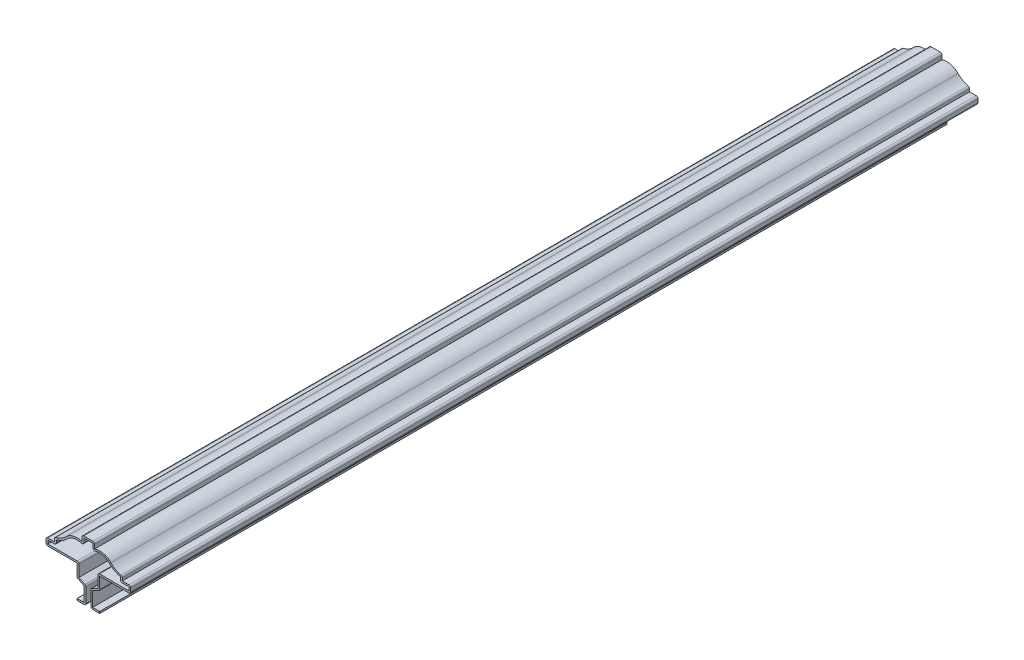
SolidWorks part; units mm, degrees
ref_plane "Front Plane" through (0, 0, 0) normal (0, 0, 1) x (1, 0, 0)
ref_plane "Top Plane" through (0, 0, 0) normal (0, 1, 0) x (1, 0, 0)
ref_plane "Right Plane" through (0, 0, 0) normal (1, 0, 0) x (0, 0, -1)
sketch "Sketch1" plane through (0, 0, 0) normal (0, 0, 1) x (1, 0, 0)
  line L0 (0, 0) -> (0, 32.3215) construction
  line L1 (-6.35, 0) -> (-2.3813, 0)
  line L2 (-2.3813, 0) -> (-2.3813, 8.1121)
  line L3 (-2.3813, 8.1121) -> (-6.35, 10.0965)
  line L4 (-6.35, 10.0965) -> (-6.35, 17.2402)
  line L5 (-6.35, 17.2402) -> (-23.8125, 17.2402)
  line L6 (-23.8125, 17.2402) -> (-23.8125, 21.209)
  line L7 (-23.8125, 21.209) -> (-19.05, 21.209)
  line L8 (-19.05, 21.209) -> (-19.05, 23.5902)
  line L9 (3.5719, 32.3215) -> (-3.5719, 32.3215)
  line L10 (-3.5719, 32.3215) -> (-3.5719, 29.0896)
  line L11 (6.35, 0) -> (2.3813, 0)
  line L12 (2.3813, 0) -> (2.3813, 8.1121)
  line L13 (2.3813, 8.1121) -> (6.35, 10.0965)
  line L14 (6.35, 10.0965) -> (6.35, 17.2402)
  line L15 (6.35, 17.2402) -> (23.8125, 17.2402)
  line L16 (23.8125, 17.2402) -> (23.8125, 21.209)
  line L17 (23.8125, 21.209) -> (19.05, 21.209)
  line L18 (19.05, 21.209) -> (19.05, 23.5902)
  line L19 (3.5719, 32.3215) -> (3.5719, 29.0896)
  arc A0 (-19.05, 23.5902) -> (-12.6337, 26.8742) centre (-20.6312, 34.5897) ccw
  arc A1 (-12.6337, 26.8742) -> (-3.5719, 29.0896) centre (-6.35, 20.8121) cw
  arc A2 (19.05, 23.5902) -> (12.6337, 26.8742) centre (20.6312, 34.5897) cw
  arc A3 (12.6337, 26.8742) -> (3.5719, 29.0896) centre (6.35, 20.8121) ccw
  point P1 (-8.4239, 0)
  point P18 (0, 0)
  point P19 (0.0427, 26.9391)
  point P20 (-2.3813, 9.1281)
  point P21 (-6.35, 12.5794)
  point P22 (-17.5022, 22.8855)
  point P23 (-11.4275, 24.6745)
  point P24 (-8.7236, 24.8236)
  point P25 (-3.5719, 28.6026)
  point P26 (-13.996, 22.225)
  point P27 (-13.1405, 27.8486)
  point P28 (0, 0)
  point P45 (6.35, 30.5594)
extrude "Extrude-Thin2" add sketch "Sketch1" against normal blind 476.25 thin
fillet "Fillet1" radius 1.016 20 edges at (-23.8125, 17.2402, -238.125) (-23.8125, 21.209, -238.125) (-19.05, 23.5902, -238.125) (-18.034, 20.193, -238.125) (-6.35, 10.0965, -238.125) (-1.3653, 8.74, -238.125) (-1.3653, -1.016, -238.125) (1.3653, -1.016, -238.125) (1.3653, 8.74, -238.125) (6.35, 10.0965, -238.125) (23.8125, 17.2402, -238.125) (23.8125, 21.209, -238.125) (18.034, 20.193, -238.125) (19.05, 23.5902, -238.125) (5.334, 18.2562, -238.125) (-5.334, 18.2562, -238.125) (-2.5559, 27.53, -238.125) (2.5559, 27.53, -238.125) (3.5719, 32.3215, -238.125) (-3.5719, 32.3215, -238.125)
equation "\"D1@Extrude-Thin2\"=\"D1@Sketch1\"*10"
